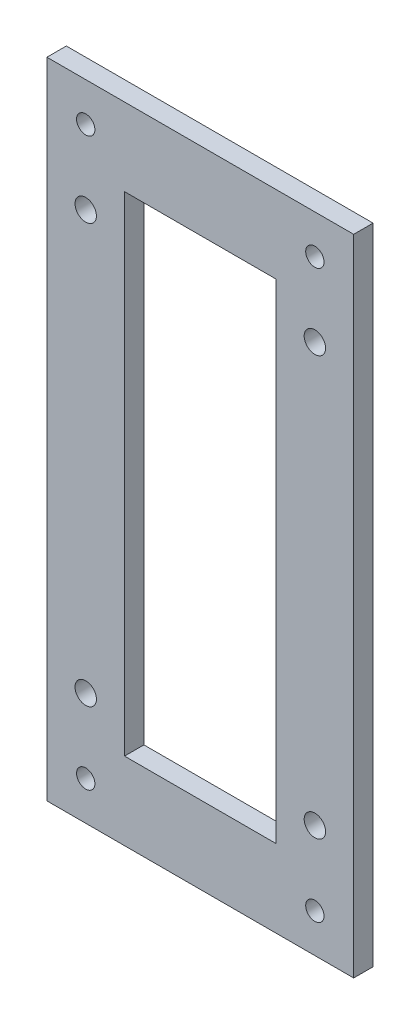
SolidWorks part; units mm, degrees
ref_plane "Front Plane" through (0, 0, 0) normal (0, 0, 1) x (1, 0, 0)
ref_plane "Top Plane" through (0, 0, 0) normal (0, 1, 0) x (1, 0, 0)
ref_plane "Right Plane" through (0, 0, 0) normal (1, 0, 0) x (0, 0, -1)
sketch "Sketch1" plane through (0, 0, 0) normal (0, 0, 1) x (1, 0, 0)
  line L1 (0, 0) -> (100.4, 0)
  line L2 (0, 0) -> (0, 210.8)
  line L3 (0, 210.8) -> (100.4, 210.8)
  line L4 (100.4, 0) -> (100.4, 210.8)
  line L5 (25.4, 185.4) -> (75, 185.4)
  line L6 (25.4, 185.4) -> (25.4, 25.4)
  line L7 (25.4, 25.4) -> (75, 25.4)
  line L8 (75, 185.4) -> (75, 25.4)
  dimension "D1" = 100.4
  dimension "D2" = 210.8
  dimension "D3" = 25.4
  dimension "D4" = 25.4
  dimension "D5" = 25.4
  dimension "D6" = 25.4
extrude "Boss-Extrude1" add sketch "Sketch1" along normal blind 6.35
sketch "Sketch2" plane through (0, 0, 6.35) normal (0, 0, 1) x (1, 0, 0)
  line L0 (0, 105.4) -> (100.4, 105.4) construction
  line L1 (0, 210.8) -> (0, 0) construction
  line L2 (100.4, 0) -> (100.4, 210.8) construction
  line L3 (50.2, 210.8) -> (50.2, 0) construction
  line L4 (100.4, 210.8) -> (0, 210.8) construction
  line L5 (0, 0) -> (100.4, 0) construction
  circle A0 centre (12.7027, 198.1) radius 3
  circle A1 centre (87.6973, 198.1) radius 3
  circle A2 centre (87.6973, 12.7) radius 3
  circle A3 centre (12.7027, 12.7) radius 3
  dimension "D1" = 6
  dimension "D2" = 12.7
  dimension "D3" = 12.7027
extrude "Cut-Extrude1" cut sketch "Sketch2" against normal blind 6.35
sketch "Sketch3" plane through (0, 0, 6.35) normal (0, 0, 1) x (1, 0, 0)
  line L0 (50.2, 173.9) -> (50.2, 36.9) construction
  line L1 (12.7, 173.9) -> (87.7, 173.9) construction
  line L2 (12.7, 173.9) -> (12.7, 36.9) construction
  line L3 (12.7, 36.9) -> (87.7, 36.9) construction
  line L4 (87.7, 173.9) -> (87.7, 36.9) construction
  line L5 (87.7, 105.4) -> (12.7, 105.4) construction
  line L6 (50.2, 210.8) -> (50.2, 0) construction
  line L7 (100.4, 210.8) -> (0, 210.8) construction
  line L8 (0, 0) -> (100.4, 0) construction
  line L9 (100.4, 105.4) -> (0, 105.4) construction
  line L10 (100.4, 0) -> (100.4, 210.8) construction
  line L11 (0, 210.8) -> (0, 0) construction
  circle A0 centre (12.7, 173.9) radius 3.5
  circle A1 centre (87.7, 173.9) radius 3.5
  circle A2 centre (87.7, 36.9) radius 3.5
  circle A3 centre (12.7, 36.9) radius 3.5
  point P20 (50.2, 105.4)
  point P21 (50.2, 105.4)
  dimension "D3" = 7
  dimension "D1" = 75
  dimension "D2" = 137
extrude "Cut-Extrude2" cut sketch "Sketch3" against normal blind 10
